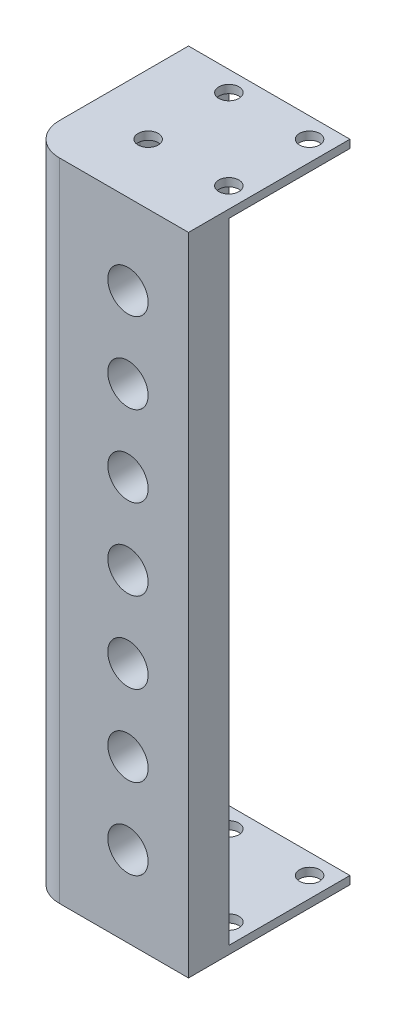
SolidWorks part; units mm, degrees
ref_plane "Front Plane" through (0, 0, 0) normal (0, 0, 1) x (1, 0, 0)
ref_plane "Top Plane" through (0, 0, 0) normal (0, 1, 0) x (1, 0, 0)
ref_plane "Right Plane" through (0, 0, 0) normal (1, 0, 0) x (0, 0, -1)
sketch "Sketch2" plane through (0, 0, 0) normal (0, 1, 0) x (1, 0, 0)
  line L1 (0, 0) -> (50.8, 0)
  line L2 (0, 0) -> (0, 50.8)
  line L3 (0, 50.8) -> (12.7, 50.8)
  line L4 (50.8, 0) -> (50.8, 12.7)
  line L7 (50.8, 12.7) -> (12.7, 12.7)
  line L8 (12.7, 50.8) -> (12.7, 12.7)
  point P8 (31.75, 12.7)
  dimension "D1" = 50.8
  dimension "D2" = 50.8
  dimension "D3" = 12.7
  dimension "D4" = 12.7
extrude "Boss-Extrude1" add sketch "Sketch2" along normal blind 203.2
fillet "Fillet1" radius 10.16 2 edges at (0, 101.6, 0) (12.7, 101.6, -12.7)
sketch "Sketch3" plane through (0, 0, 0) normal (0, 0, 1) x (1, 0, 0)
  line L0 (10.16, 203.2) -> (50.8, 203.2) construction
  line L1 (50.8, 203.2) -> (50.8, 0) construction
  line L2 (10.16, 0) -> (50.8, 0) construction
  circle A0 centre (31.75, 177.8) radius 6.35
  circle A1 centre (31.75, 152.4) radius 6.35
  circle A2 centre (31.75, 127) radius 6.35
  circle A3 centre (31.75, 101.6) radius 6.35
  circle A4 centre (31.75, 76.2) radius 6.35
  circle A5 centre (31.75, 50.8) radius 6.35
  circle A6 centre (31.75, 25.4) radius 6.35
  dimension "D1" = 12.7
  dimension "D2" = 25.4
  dimension "D3" = 19.05
  dimension "D5" = 25.4
  dimension "D4" = 7
extrude "Cut-Extrude1" cut sketch "Sketch3" against normal through all
sketch "Sketch4" plane through (0, 0, 0) normal (-1, 0, 0) x (0, 0, 1)
  line L0 (-50.8, 203.2) -> (-50.8, 0) construction
  line L1 (-50.8, 203.2) -> (-10.16, 203.2) construction
  circle A0 centre (-31.75, 177.8) radius 6.35
  circle A1 centre (-31.75, 152.4) radius 6.35
  circle A2 centre (-31.75, 127) radius 6.35
  circle A3 centre (-31.75, 101.6) radius 6.35
  circle A4 centre (-31.75, 76.2) radius 6.35
  circle A5 centre (-31.75, 50.8) radius 6.35
  circle A6 centre (-31.75, 25.4) radius 6.35
  dimension "D1" = 12.7
  dimension "D2" = 19.05
  dimension "D3" = 25.4
  dimension "D4" = 7
extrude "Cut-Extrude2" cut sketch "Sketch4" against normal through all
sketch "Sketch5" plane through (0, 203.2, 0) normal (0, 1, 0) x (1, 0, 0)
  line L1 (12.7, 50.8) -> (50.8, 50.8)
  line L4 (50.8, 50.8) -> (50.8, 12.7)
  line L5 (12.7, 50.8) -> (50.8, 50.8)
  line L6 (12.7, 50.8) -> (12.7, 12.7)
  line L7 (12.7, 12.7) -> (50.8, 12.7)
  line L8 (50.8, 50.8) -> (50.8, 12.7)
  circle A0 centre (19.05, 44.45) radius 3.175
  circle A1 centre (44.45, 44.45) radius 3.175
  circle A2 centre (44.45, 19.05) radius 3.175
  circle A3 centre (19.05, 19.05) radius 3.175
  point P4 (0, 0)
  dimension "D1" = 6.35
  dimension "D2" = 6.35
  dimension "D5" = 6.35
  dimension "D3" = 2
  dimension "D4" = 2
extrude "Boss-Extrude2" add sketch "Sketch5" against normal blind 2.54
ref_plane "Mirror Plane" through (0, 101.6, 0) normal (0, 1, 0) x (1, 0, 0)
mirror "Mirror1" about plane through (0, 101.6, 0) normal (0, 1, 0) of "Boss-Extrude2"
